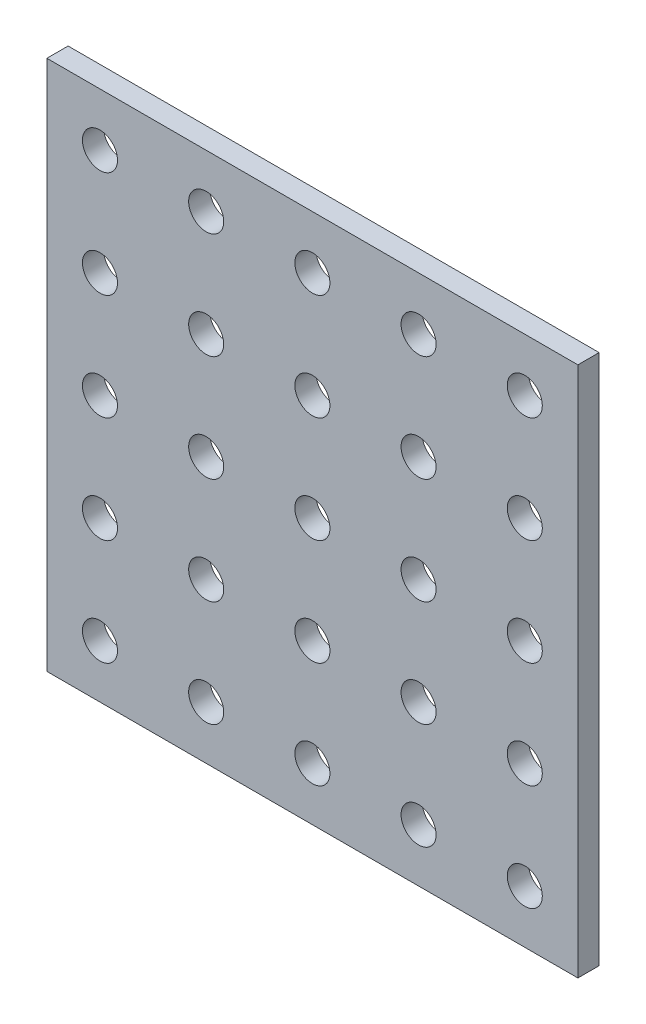
SolidWorks part; units mm, degrees
ref_plane "Front Plane" through (0, 0, 0) normal (0, 0, 1) x (1, 0, 0)
ref_plane "Top Plane" through (0, 0, 0) normal (0, 1, 0) x (1, 0, 0)
ref_plane "Right Plane" through (0, 0, 0) normal (1, 0, 0) x (0, 0, -1)
sketch "Sketch1" plane through (0, 0, 0) normal (0, 0, 1) x (1, 0, 0)
  line L1 (-25, -25) -> (25, -25)
  line L2 (-25, -25) -> (-25, 25)
  line L3 (-25, 25) -> (25, 25)
  line L4 (25, -25) -> (25, 25)
  line L5 (-25, -25) -> (25, 25) construction
  line L6 (-25, 25) -> (25, -25) construction
  point P0 (0, 0)
  dimension "D1" = 50
  dimension "D2" = 50
extrude "Boss-Extrude1" add sketch "Sketch1" along normal blind 2
sketch "Sketch2" plane through (0, 0, 2) normal (0, 0, 1) x (1, 0, 0)
  line L0 (-25, 25) -> (-25, -25) construction
  line L2 (25, 25) -> (-25, 25) construction
  circle A0 centre (-20, 20) radius 1.65
  dimension "D1" = 3.3
  dimension "D2" = 5
  dimension "D3" = 5
extrude "Cut-Extrude1" cut sketch "Sketch2" against normal through all
pattern_linear "LPattern1" count 5 spacing 10 along (0, -1, 0) count 5 spacing 10 along (1, 0, 0) of "Cut-Extrude1"
